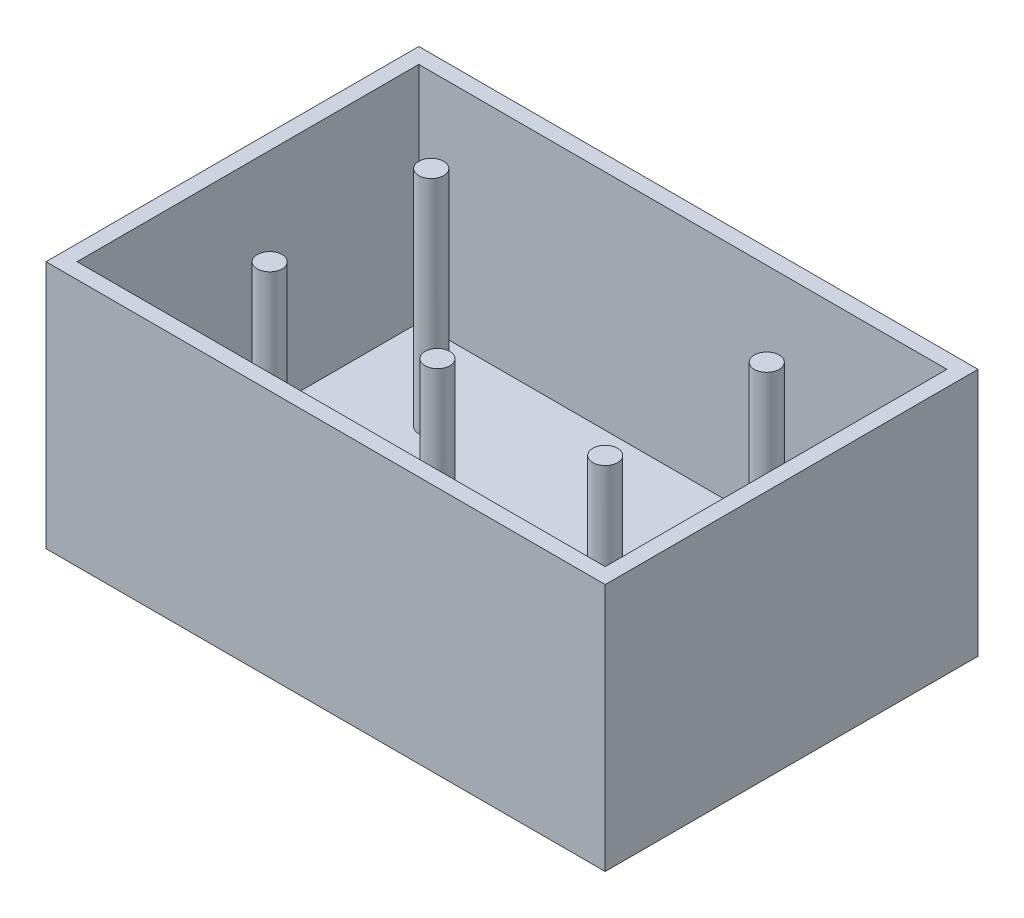
SolidWorks part; units mm, degrees
ref_plane "Front Plane" through (0, 0, 0) normal (0, 0, 1) x (1, 0, 0)
ref_plane "Top Plane" through (0, 0, 0) normal (0, 1, 0) x (1, 0, 0)
ref_plane "Right Plane" through (0, 0, 0) normal (1, 0, 0) x (0, 0, -1)
sketch "Sketch3" plane through (0, 0, 0) normal (0, 1, 0) x (1, 0, 0)
  line L0 (0, 0) -> (0, 17.78) construction
  line L1 (57.15, -38.1) -> (-57.15, -38.1)
  line L2 (57.15, -38.1) -> (57.15, 38.1)
  line L3 (57.15, 38.1) -> (-57.15, 38.1)
  line L4 (-57.15, -38.1) -> (-57.15, 38.1)
  line L5 (57.15, -38.1) -> (-57.15, 38.1) construction
  line L6 (57.15, 38.1) -> (-57.15, -38.1) construction
  line L7 (12.7, 17.78) -> (-12.7, 17.78) construction
  circle A5 centre (-34.29, -15.24) radius 2.54
  circle A6 centre (0, -15.24) radius 2.54
  circle A7 centre (34.29, -15.24) radius 2.54
  circle A9 centre (-34.29, -15.24) radius 15.5575 construction
  circle A10 centre (0, -15.24) radius 15.5575 construction
  circle A11 centre (34.29, -15.24) radius 15.5575 construction
  circle A13 centre (-34.29, 17.78) radius 2.54
  circle A14 centre (-34.29, 17.78) radius 15.5575 construction
  circle A15 centre (34.29, 17.78) radius 2.54
  circle A16 centre (34.29, 17.78) radius 15.5575 construction
  point P0 (0, 0)
  point P13 (0, 17.78)
  point P20 (0, 17.78)
  point P21 (-12.7212, 17.78)
  point P22 (34.29, -15.24)
  dimension "D3" = 5.08
  dimension "D5" = 31.115
  dimension "D4" = 22.86
  dimension "D7" = 22.86
  dimension "D1" = 114.3
  dimension "D2" = 76.2
  dimension "D6" = 22.86
  dimension "D8" = 20.32
  dimension "D9" = 25.4
sketch "Sketch4" plane through (0, 0, 0) normal (0, 1, 0) x (1, 0, 0)
  line L0 (57.15, -38.1) -> (57.15, 38.1) construction
  line L1 (57.15, -38.1) -> (-57.15, -38.1) construction
  line L2 (-57.15, -38.1) -> (-57.15, 38.1) construction
  line L3 (57.15, 38.1) -> (-57.15, 38.1) construction
  line L4 (57.15, -38.1) -> (57.15, 38.1)
  line L5 (57.15, -38.1) -> (-57.15, -38.1)
  line L6 (-57.15, -38.1) -> (-57.15, 38.1)
  line L7 (57.15, 38.1) -> (-57.15, 38.1)
extrude "Boss-Extrude2" add sketch "Sketch4" along normal mid plane 50.8
ref_plane "Plane1" through (0, -20.32, 0) normal (0, -1, 0) x (-1, 0, 0)
sketch "Sketch5" plane through (0, -20.32, 0) normal (0, -1, 0) x (-1, 0, 0)
  line L0 (-57.15, -38.1) -> (57.15, -38.1) construction
  line L1 (57.15, -38.1) -> (57.15, 38.1) construction
  line L2 (-57.15, 38.1) -> (57.15, 38.1) construction
  line L3 (-57.15, -38.1) -> (-57.15, 38.1) construction
  line L4 (-57.15, -38.1) -> (57.15, -38.1) construction
  line L5 (57.15, -38.1) -> (57.15, 38.1) construction
  line L6 (-57.15, 38.1) -> (57.15, 38.1) construction
  line L7 (-57.15, -38.1) -> (-57.15, 38.1) construction
  line L9 (53.975, -34.925) -> (-53.975, -34.925)
  line L10 (53.975, -34.925) -> (53.975, 34.925)
  line L11 (53.975, 34.925) -> (-53.975, 34.925)
  line L12 (-53.975, -34.925) -> (-53.975, 34.925)
  line L13 (53.975, -34.925) -> (-53.975, 34.925) construction
  line L14 (53.975, 34.925) -> (-53.975, -34.925) construction
  point P2 (0, 0)
  dimension "D1" = 3.175
  dimension "D2" = 3.175
extrude "Cut-Extrude1" cut sketch "Sketch5" against normal up to next
sketch "Sketch6" plane through (0, 0, 0) normal (0, 1, 0) x (1, 0, 0)
  circle A0 centre (34.29, 17.78) radius 2.54 construction
  circle A1 centre (34.29, -15.24) radius 2.54 construction
  circle A2 centre (0, -15.24) radius 2.54 construction
  circle A3 centre (-34.29, -15.24) radius 2.54 construction
  circle A4 centre (-34.29, 17.78) radius 2.54 construction
  circle A5 centre (34.29, 17.78) radius 2.54
  circle A6 centre (34.29, -15.24) radius 2.54
  circle A7 centre (0, -15.24) radius 2.54
  circle A8 centre (-34.29, -15.24) radius 2.54
  circle A9 centre (-34.29, 17.78) radius 2.54
extrude "Boss-Extrude3" add sketch "Sketch6" along normal mid plane 50.8
